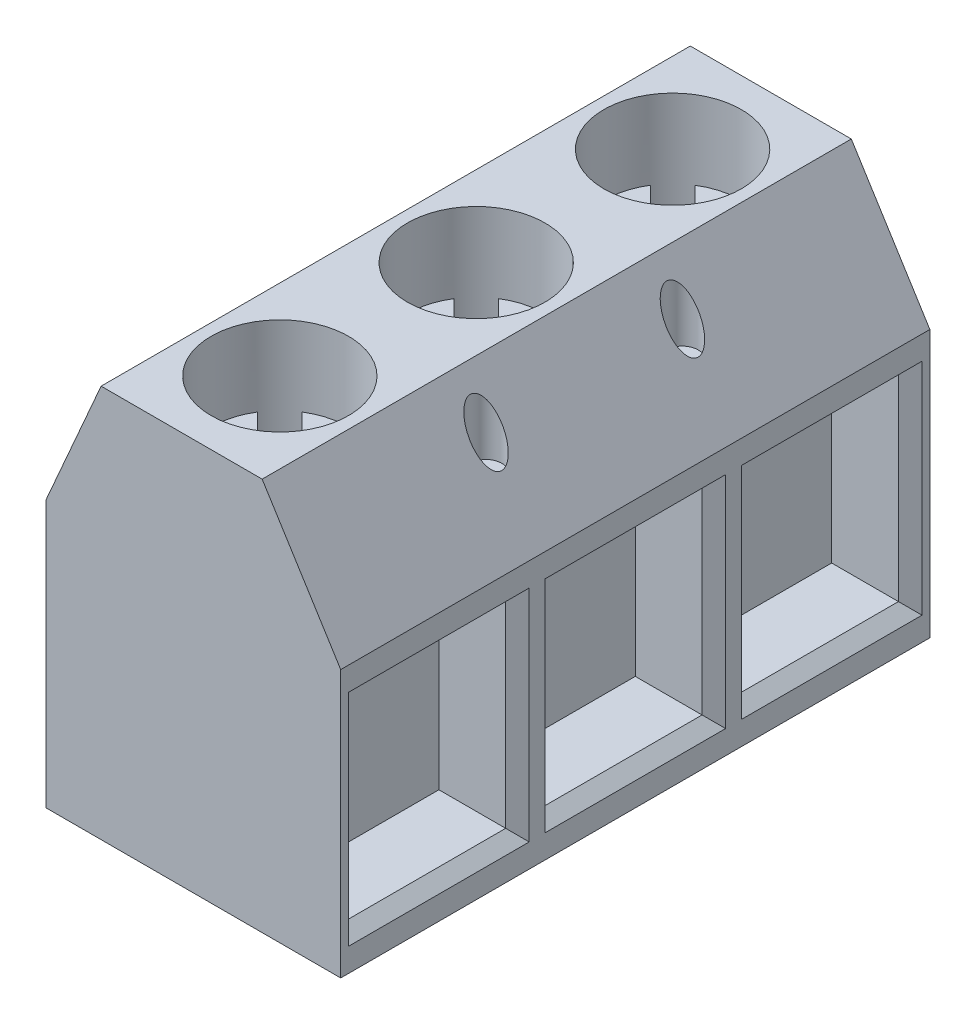
SolidWorks part; units mm, degrees
ref_plane "Front Plane" through (0, 0, 0) normal (0, 0, 1) x (1, 0, 0)
ref_plane "Top Plane" through (0, 0, 0) normal (0, 1, 0) x (1, 0, 0)
ref_plane "Right Plane" through (0, 0, 0) normal (1, 0, 0) x (0, 0, -1)
sketch "Sketch1" plane through (0, 0, 0) normal (0, 0, 1) x (1, 0, 0)
  line L0 (-3.75, 0) -> (3.75, 0)
  line L1 (3.75, 0) -> (3.75, 6.8)
  line L2 (3.75, 6.8) -> (1.75, 10)
  line L3 (1.75, 10) -> (-2.35, 10)
  line L4 (-3.75, 0) -> (-3.75, 6.8)
  line L5 (-2.35, 10) -> (-3.75, 6.8)
  dimension "D1" = 1.4
  dimension "D2" = 7.5
  dimension "D3" = 10
  dimension "D4" = 2
  dimension "D5" = 6.8
extrude "Boss-Extrude1" add sketch "Sketch1" along normal mid plane 15
sketch "Sketch2" plane through (0, 0, 0) normal (0, -1, 0) x (1, 0, 0)
  line L0 (0.45, 4.5) -> (0.45, 0) construction
  line L1 (-0.05, 5.5) -> (0.95, 5.5)
  line L2 (-0.05, 5.5) -> (-0.05, 4.5)
  line L3 (-0.05, 4.5) -> (0.95, 4.5)
  line L4 (0.95, 5.5) -> (0.95, 4.5)
  line L5 (-0.05, 0.5) -> (0.95, 0.5)
  line L6 (-0.05, 0.5) -> (-0.05, -0.5)
  line L7 (-0.05, -0.5) -> (0.95, -0.5)
  line L8 (0.95, 0.5) -> (0.95, -0.5)
  line L9 (-0.05, -4.5) -> (0.95, -4.5)
  line L10 (-0.05, -4.5) -> (-0.05, -5.5)
  line L11 (-0.05, -5.5) -> (0.95, -5.5)
  line L12 (0.95, -4.5) -> (0.95, -5.5)
  line L13 (0.45, -4.5) -> (0.45, -0.5) construction
  line L14 (0.95, 5) -> (3.5135, 5) construction
  line L15 (0.95, 0) -> (0, 0) construction
  line L16 (0.95, -5) -> (2.7662, -5) construction
  line L17 (0.95, -0.5) -> (-0.05, 0.5) construction
  line L18 (3.75, 7.5) -> (3.75, -7.5) construction
  dimension "D1" = 5
  dimension "D2" = 5
  dimension "D3" = 1
  dimension "D4" = 3.3
extrude "Boss-Extrude2" add sketch "Sketch2" along normal blind 1
sketch "Sketch3" plane through (3.75, 0, 0) normal (1, 0, 0) x (0, 0, -1)
  line L0 (5, 0.9) -> (5, -1) construction
  line L1 (-7, 5.9) -> (-3, 5.9)
  line L2 (-7, 5.9) -> (-7, 0.9)
  line L3 (-7, 0.9) -> (-3, 0.9)
  line L4 (-3, 5.9) -> (-3, 0.9)
  line L5 (-2, 5.9) -> (2, 5.9)
  line L6 (-2, 5.9) -> (-2, 0.9)
  line L7 (-2, 0.9) -> (2, 0.9)
  line L8 (2, 5.9) -> (2, 0.9)
  line L9 (3, 5.9) -> (7, 5.9)
  line L10 (3, 5.9) -> (3, 0.9)
  line L11 (3, 0.9) -> (7, 0.9)
  line L12 (7, 5.9) -> (7, 0.9)
  line L13 (5.5, -1) -> (4.5, -1) construction
  line L14 (-5, 0.9) -> (-5, -1) construction
  line L15 (-4.5, -1) -> (-5.5, -1) construction
  line L16 (0, 0.9) -> (0, 0) construction
  line L17 (-7.5, 0) -> (7.5, 0) construction
  dimension "D1" = 4
  dimension "D2" = 5
  dimension "D3" = 0.9
extrude "Cut-Extrude1" cut sketch "Sketch3" against normal blind 2
sketch "Sketch4" plane through (0, 10, 0) normal (0, 1, 0) x (1, 0, 0)
  line L0 (-0.3, 5) -> (-0.3, 0) construction
  line L1 (-0.3, 0) -> (-0.3, -5) construction
  line L2 (-0.3, 0) -> (0, 0) construction
  line L3 (-0.3, 5) -> (-0.3, 7.5) construction
  line L4 (1.75, 7.5) -> (-2.35, 7.5) construction
  line L5 (2.45, 2.5) -> (-3.05, 2.5) construction
  line L6 (2.45, -2.5) -> (-3.05, -2.5) construction
  line L7 (-3.05, 2.5) -> (-3.05, -2.5) construction
  circle A0 centre (-0.3, 5) radius 1.75
  circle A1 centre (-0.3, 0) radius 1.75
  circle A2 centre (-0.3, -5) radius 1.75
  circle A3 centre (2.45, 2.5) radius 0.4
  circle A4 centre (2.45, -2.5) radius 0.4
  circle A5 centre (-3.05, 2.5) radius 0.4
  circle A6 centre (-3.05, -2.5) radius 0.4
  dimension "D1" = 3.5
  dimension "D3" = 5
  dimension "D4" = 0.8
  dimension "D8" = 2.75
  dimension "D2" = 5
  dimension "D5" = 5
  dimension "D6" = 2.5
  dimension "D7" = 5.5
extrude "Cut-Extrude2" cut sketch "Sketch4" against normal blind 2
sketch "Sketch5" plane through (0, 8, 0) normal (0, 1, 0) x (1, 0, 0)
  line L0 (-0.3, 5) -> (-1.5374, 6.2374) construction
  line L1 (-1.2218, 1.4875) -> (-0.3, 0.5657)
  line L2 (-0.3, 0.5657) -> (0.1243, 0.9899)
  line L3 (-0.3, 5) -> (0.4071, 5.7071) construction
  line L4 (-1.2218, 6.4875) -> (-0.3, 5.5657)
  line L5 (0.6218, 3.5125) -> (-0.3, 4.4343)
  line L6 (0.1243, 0.9899) -> (0.6899, 0.4243)
  line L7 (0.6899, 0.4243) -> (0.2657, 0)
  line L8 (0.2657, 0) -> (1.1875, -0.9218)
  line L9 (0.6218, -1.4875) -> (-0.3, -0.5657)
  line L10 (-3.75, -7.5) -> (-3.75, 7.5) construction
  line L11 (-0.3, 5.5657) -> (0.1243, 5.9899)
  line L12 (0.1243, 5.9899) -> (0.6899, 5.4243)
  line L13 (0.6899, 5.4243) -> (0.2657, 5)
  line L14 (-0.3, 4.4343) -> (-0.7243, 4.0101)
  line L15 (-0.7243, 4.0101) -> (-1.2899, 4.5757)
  line L16 (-1.2899, 4.5757) -> (-0.8657, 5)
  line L17 (0.2657, 5) -> (1.1875, 4.0782)
  line L18 (-0.8657, 5) -> (-1.7875, 5.9218)
  line L19 (-0.3, -0.5657) -> (-0.7243, -0.9899)
  line L20 (-0.7243, -0.9899) -> (-1.2899, -0.4243)
  line L21 (-1.2899, -0.4243) -> (-0.8657, 0)
  line L22 (-0.8657, 0) -> (-1.7875, 0.9218)
  line L23 (-1.2218, -3.5125) -> (-0.3, -4.4343)
  line L24 (-0.3, -4.4343) -> (0.1243, -4.0101)
  line L25 (0.1243, -4.0101) -> (0.6899, -4.5757)
  line L26 (0.6899, -4.5757) -> (0.2657, -5)
  line L27 (0.2657, -5) -> (1.1875, -5.9218)
  line L28 (0.6218, -6.4875) -> (-0.3, -5.5657)
  line L29 (-0.3, -5.5657) -> (-0.7243, -5.9899)
  line L30 (-0.7243, -5.9899) -> (-1.2899, -5.4243)
  line L31 (-1.2899, -5.4243) -> (-0.8657, -5)
  line L32 (-0.8657, -5) -> (-1.7875, -4.0782)
  arc A0 (-1.2218, 6.4875) -> (-1.7875, 5.9218) centre (-0.3, 5) ccw
  circle A1 centre (-0.3, 5) radius 1.75 construction
  arc A2 (-1.2218, 1.4875) -> (-1.7875, 0.9218) centre (-0.3, 0) ccw
  arc A4 (0.6218, 3.5125) -> (1.1875, 4.0782) centre (-0.3, 5) ccw
  arc A5 (0.6218, -1.4875) -> (1.1875, -0.9218) centre (-0.3, 0) ccw
  arc A6 (-1.2218, -3.5125) -> (-1.7875, -4.0782) centre (-0.3, -5) ccw
  arc A7 (0.6218, -6.4875) -> (1.1875, -5.9218) centre (-0.3, -5) ccw
  dimension "D1" = 45
  dimension "D2" = 0.8
  dimension "D3" = 2
  dimension "D4" = 0.8
  dimension "D5" = 3
extrude "Cut-Extrude3" cut sketch "Sketch5" against normal blind 0.5
chamfer "Chamfer1" distance 0.3 angle 45 12 edges at (3.75, 3.4, 3) (3.75, 5.9, 5) (3.75, 3.4, 7) (3.75, 0.9, 5) (3.75, 3.4, -2) (3.75, 5.9, 0) (3.75, 3.4, 2) (3.75, 0.9, 0) (3.75, 3.4, -7) (3.75, 5.9, -5) (3.75, 3.4, -3) (3.75, 0.9, -5)
